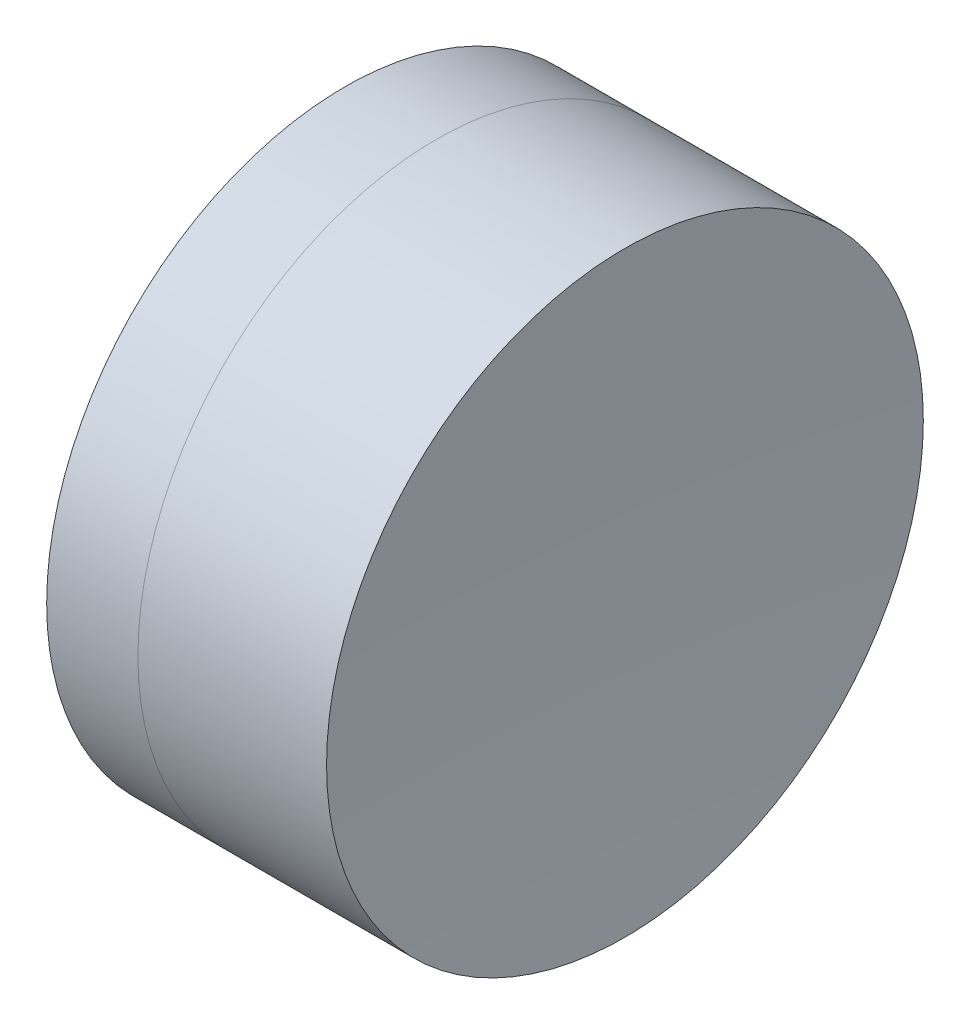
SolidWorks part; units mm, degrees
ref_plane "前视基准面" through (0, 0, 0) normal (0, 0, 1) x (1, 0, 0)
ref_plane "上视基准面" through (0, 0, 0) normal (0, 1, 0) x (1, 0, 0)
ref_plane "右视基准面" through (0, 0, 0) normal (1, 0, 0) x (0, 0, -1)
sketch "草图1" plane through (0, 0, 0) normal (0, 1, 0) x (1, 0, 0)
  line L0 (-0.8161, 0) -> (26.6816, 0) construction
  line L1 (21.8762, -4) -> (23.0992, -4)
  line L2 (21.8762, 4) -> (23.0992, 4)
  arc A0 (23.0992, -4) -> (23.0992, 4) centre (16.4613, 0) ccw
  arc A1 (21.8762, 4) -> (21.8762, -4) centre (28.1613, 0) ccw
  point P10 (20.7113, 0)
  point P11 (24.2113, 0)
  dimension "D3" = 7.45
  dimension "D4" = 7.75
  dimension "D1" = 4
  dimension "D2" = 4
  dimension "D5" = 3.5
revolve "旋转1" add sketch "草图1" angle 360 about L0
sketch "草图2" plane through (0, 0, 0) normal (0, 1, 0) x (1, 0, 0)
  line L0 (-0.5519, 0) -> (34.9089, 0) construction
  line L2 (23.0992, 4) -> (25.6281, 4)
  line L3 (23.0992, -4) -> (25.6281, -4)
  arc A0 (25.6281, 4) -> (25.6281, -4) centre (94.0513, 0) ccw
  arc A1 (23.0992, -4) -> (23.0992, 4) centre (16.4613, 0) ccw construction
  arc A2 (23.0992, -4) -> (23.0992, 4) centre (16.4613, 0) ccw
  point P4 (24.2113, 0)
  point P8 (25.5113, 0)
  dimension "D1" = 68.54
  dimension "D2" = 1.3
revolve "旋转2" add sketch "草图2" angle 360 about L0
